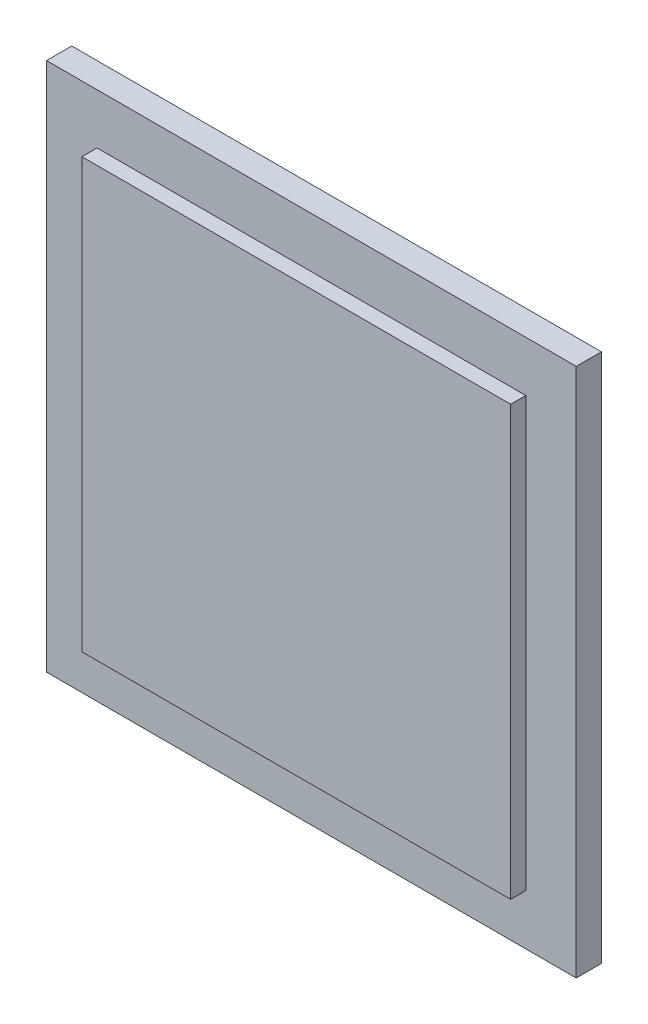
SolidWorks part; units mm, degrees
ref_plane "Front Plane" through (0, 0, 0) normal (0, 0, 1) x (1, 0, 0)
ref_plane "Top Plane" through (0, 0, 0) normal (0, 1, 0) x (1, 0, 0)
ref_plane "Right Plane" through (0, 0, 0) normal (1, 0, 0) x (0, 0, -1)
sketch "Sketch1" plane through (0, 0, 0) normal (0, 0, 1) x (1, 0, 0)
  line L1 (-52.5, 52.5) -> (52.5, 52.5)
  line L2 (-52.5, 52.5) -> (-52.5, -52.5)
  line L3 (-52.5, -52.5) -> (52.5, -52.5)
  line L4 (52.5, 52.5) -> (52.5, -52.5)
  line L5 (-52.5, 52.5) -> (52.5, -52.5) construction
  line L6 (-52.5, -52.5) -> (52.5, 52.5) construction
  point P0 (0, 0)
  dimension "D1" = 105
  dimension "D2" = 105
extrude "Boss-Extrude1" add sketch "Sketch1" along normal blind 5 contours L1 L4 L3 L2
sketch "Sketch2" plane through (0, 0, 5) normal (0, 0, 1) x (1, 0, 0)
  line L1 (-42.5, 42.5) -> (42.5, 42.5)
  line L2 (-42.5, 42.5) -> (-42.5, -42.5)
  line L3 (-42.5, -42.5) -> (42.5, -42.5)
  line L4 (42.5, 42.5) -> (42.5, -42.5)
  line L5 (-42.5, 42.5) -> (42.5, -42.5) construction
  line L6 (-42.5, -42.5) -> (42.5, 42.5) construction
  point P0 (0, 0)
  dimension "D1" = 85
  dimension "D2" = 85
extrude "Boss-Extrude2" add sketch "Sketch2" along normal blind 3
